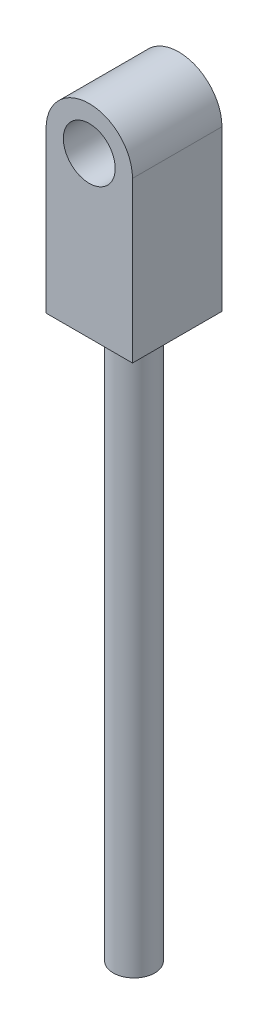
SolidWorks part; units mm, degrees
material "1.0037 (S235JR)"
ref_plane "Front Plane" through (0, 0, 0) normal (0, 0, 1) x (1, 0, 0)
ref_plane "Top Plane" through (0, 0, 0) normal (0, 1, 0) x (1, 0, 0)
ref_plane "Right Plane" through (0, 0, 0) normal (1, 0, 0) x (0, 0, -1)
sketch "Sketch1" plane through (0, 0, 0) normal (0, 0, 1) x (1, 0, 0)
  line L0 (0, 41.0584) -> (0, -37.0649) construction
  line L1 (-2.5, 0) -> (-2.5, -9.25)
  line L2 (2.5, 0) -> (2.5, -9.25)
  line L3 (-2.5, -9.25) -> (2.5, -9.25)
  circle A0 centre (0, 0) radius 1.5
  arc A1 (2.5, 0) -> (-2.5, 0) centre (0, 0) ccw
  dimension "D1" = 3
  dimension "D2" = 5
  dimension "D3" = 9.25
  dimension "D4" = 5
extrude "Boss-Extrude1" add sketch "Sketch1" along normal blind 1.725 and the other way blind 3.45
sketch "Sketch2" plane through (0, -9.25, 0) normal (0, -1, 0) x (1, 0, 0)
  line L0 (-2.5, 1.725) -> (2.5, -3.45) construction
  line L1 (2.5, 1.725) -> (-2.5, -3.45) construction
  circle A0 centre (0, -0.8625) radius 1.203
  dimension "D1" = 2.406
extrude "Boss-Extrude2" add sketch "Sketch2" along normal blind 32.5
